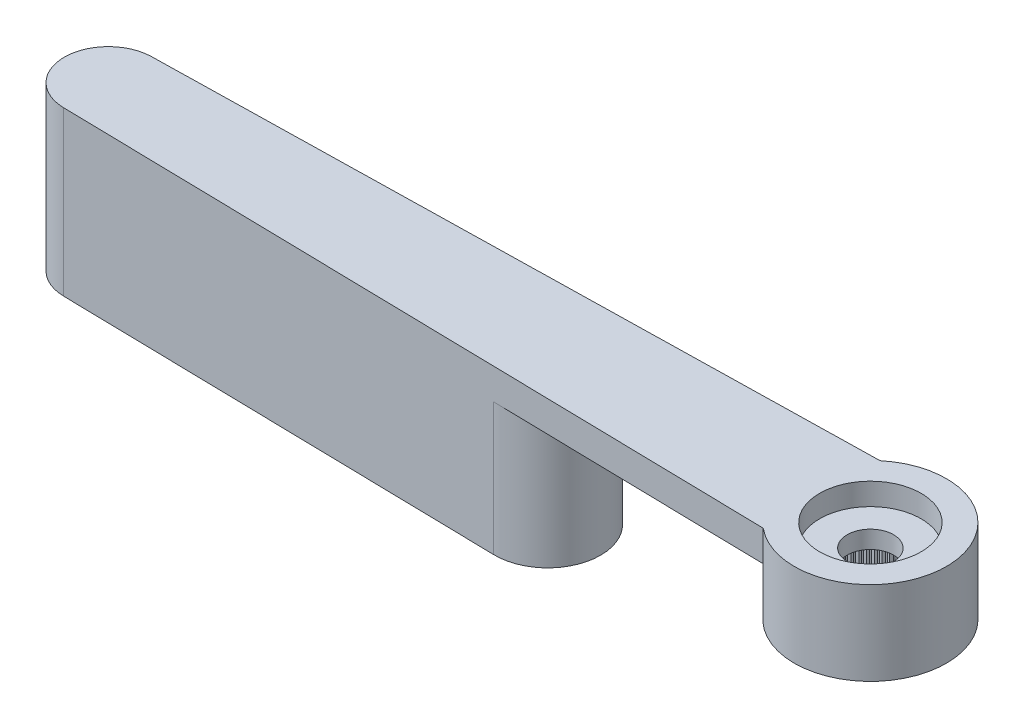
SolidWorks part; units mm, degrees
material "PVC Rígido"
ref_plane "Plano frontal" through (0, 0, 0) normal (0, 0, 1) x (1, 0, 0)
ref_plane "Plano superior" through (0, 0, 0) normal (0, 1, 0) x (1, 0, 0)
ref_plane "Plano direito" through (0, 0, 0) normal (1, 0, 0) x (0, 0, -1)
sketch "Esboço1" plane through (0, 0, 0) normal (0, 1, 0) x (1, 0, 0)
  line L0 (0, 0) -> (-34.55, 0) construction
  line L1 (-34.5902, 1.9996) -> (-2.2091, 2.65)
  line L2 (-2.2091, -2.65) -> (-34.5902, -1.9996)
  arc A0 (-2.2091, -2.65) -> (-2.2091, 2.65) centre (0, 0) ccw
  arc A1 (-34.5902, 1.9996) -> (-34.5902, -1.9996) centre (-34.55, 0) ccw
  dimension "D1" = 6.9
  dimension "D2" = 4
  dimension "D3" = 40
  dimension "D4" = 5.3
extrude "Ressalto-extrusão1" add sketch "Esboço1" against normal blind 1.4
sketch "Esboço2" plane through (0, -1.4, 0) normal (0, -1, 0) x (1, 0, 0)
  arc A0 (-2.2091, -2.65) -> (-2.2091, 2.65) centre (0, 0) ccw construction
  circle A1 centre (0, 0) radius 3.45
extrude "Ressalto-extrusão2" add sketch "Esboço2" along normal offset from surface (2.4 mm away) 3.8 up to face at (-17.4748, 0, 0)
hole_wizard "Furo1" positions "Esboço3" profile "Esboço4" legacy
sketch "Esboço3" plane through (0, -3.8, 0) normal (0, -1, 0) x (-1, 0, 0)
  point P0 (0, 0)
sketch "Esboço4" plane through (0, -3.8, 0) normal (1, 0, 0) x (0, 0, -1)
  line L0 (0, 0) -> (0, 2)
  line L1 (0, 2) -> (2.475, 2)
  line L2 (2.475, 2) -> (2.475, 0)
  line L3 (2.475, 0) -> (0, 0)
  line L4 (0, 110) -> (0, -10) construction
  dimension "Diameter" = 4.95
  dimension "Depth" = 2
hole_wizard "Furo2" positions "Esboço5" profile "Esboço6" legacy
sketch "Esboço5" plane through (0, 0, 0) normal (0, 1, 0) x (1, 0, 0)
  point P0 (0, 0)
sketch "Esboço6" plane through (0, 0, 0) normal (1, 0, 0) x (0, 0, 1)
  line L0 (0, 0) -> (0, 1)
  line L1 (0, 1) -> (2.3, 1)
  line L2 (2.3, 1) -> (2.3, 0)
  line L3 (2.3, 0) -> (0, 0)
  line L4 (0, 110) -> (0, -10) construction
  dimension "Diameter" = 4.6
  dimension "Depth" = 1
hole_wizard "Furo3" positions "Esboço7" profile "Esboço8" legacy end condition through all
sketch "Esboço7" plane through (0, 0, 0) normal (0, 1, 0) x (1, 0, 0)
  point P0 (0, 0)
sketch "Esboço8" plane through (0, 0, 0) normal (1, 0, 0) x (0, 0, 1)
  line L0 (0, 0) -> (0, 3.8)
  line L1 (0, 3.8) -> (1.05, 3.8)
  line L2 (1.05, 3.8) -> (1.05, 0)
  line L3 (1.05, 0) -> (0, 0)
  line L4 (0, 110) -> (0, -10) construction
  dimension "Diameter" = 2.1
  dimension "Depth" = 3.8
sketch "Esboço11" plane through (0, -3.8, 0) normal (0, -1, 0) x (1, 0, 0)
  line L0 (-0.0981, 2.4731) -> (0, 2.375)
  line L1 (0, 2.375) -> (0.0981, 2.4731)
  line L2 (0, 0) -> (0, 2.475) construction
  circle A0 centre (0, 0) radius 2.375 construction
  circle A1 centre (0, 0) radius 2.475
  arc A2 (0.0981, 2.4731) -> (-0.0981, 2.4731) centre (0, 0) ccw
  dimension "D3" = 4.75
  dimension "D2" = 0.1
  dimension "D1" = 0
extrude "Ressalto-extrusão3" add sketch "Esboço11" against normal up to surface (2 mm away) up to face at (0, -1.8, 1.05)
pattern_circular "PadrãoCircular1" count 60 over 360 about axis through (0, 0, 0) along (0, 1, 0) of "Ressalto-extrusão3"
sketch "Sketch1" plane through (0, -1.4, 0) normal (0, -1, 0) x (1, 0, 0)
  line L0 (-14.6496, 0.8998) -> (-34.56, 0.4999)
  line L1 (-34.56, -0.4999) -> (-14.6496, -0.8998)
  line L2 (-2.2091, 2.65) -> (-34.5902, 1.9996)
  line L3 (-34.5902, -1.9996) -> (-2.2091, -2.65)
  line L4 (-14.6797, 2.3995) -> (-34.5902, 1.9996)
  line L5 (-34.5902, -1.9996) -> (-14.6797, -2.3995)
  arc A0 (-14.6797, -2.3995) -> (-14.6797, 2.3995) centre (-14.6315, 0) ccw
  arc A1 (-34.56, 0.4999) -> (-34.56, -0.4999) centre (-34.55, 0) ccw
  arc A2 (-2.2091, 2.65) -> (-2.2091, -2.65) centre (0, 0) ccw
  arc A3 (-34.5902, 1.9996) -> (-34.5902, -1.9996) centre (-34.55, 0) ccw
  arc A4 (-2.2091, 2.65) -> (-2.2091, -2.65) centre (0, 0) ccw
  arc A5 (-34.5902, 1.9996) -> (-34.5902, -1.9996) centre (-34.55, 0) ccw
  arc A6 (-14.6496, -0.8998) -> (-14.6496, 0.8998) centre (-14.6315, 0) ccw
  line M6 (-2.2091, 2.65) -> (-34.5902, 1.9996)
  arc M7 (-34.5902, 1.9996) -> (-34.5902, -1.9996) centre (-34.55, 0) ccw
  line M8 (-34.5902, -1.9996) -> (-2.2091, -2.65)
  dimension "D2" = 4.8
  dimension "D1" = 0
  dimension "D3" = 1.5
extrude "Boss-Extrude1" add sketch "Sketch1" along normal blind 6 contours A0 M8 M6 M7
